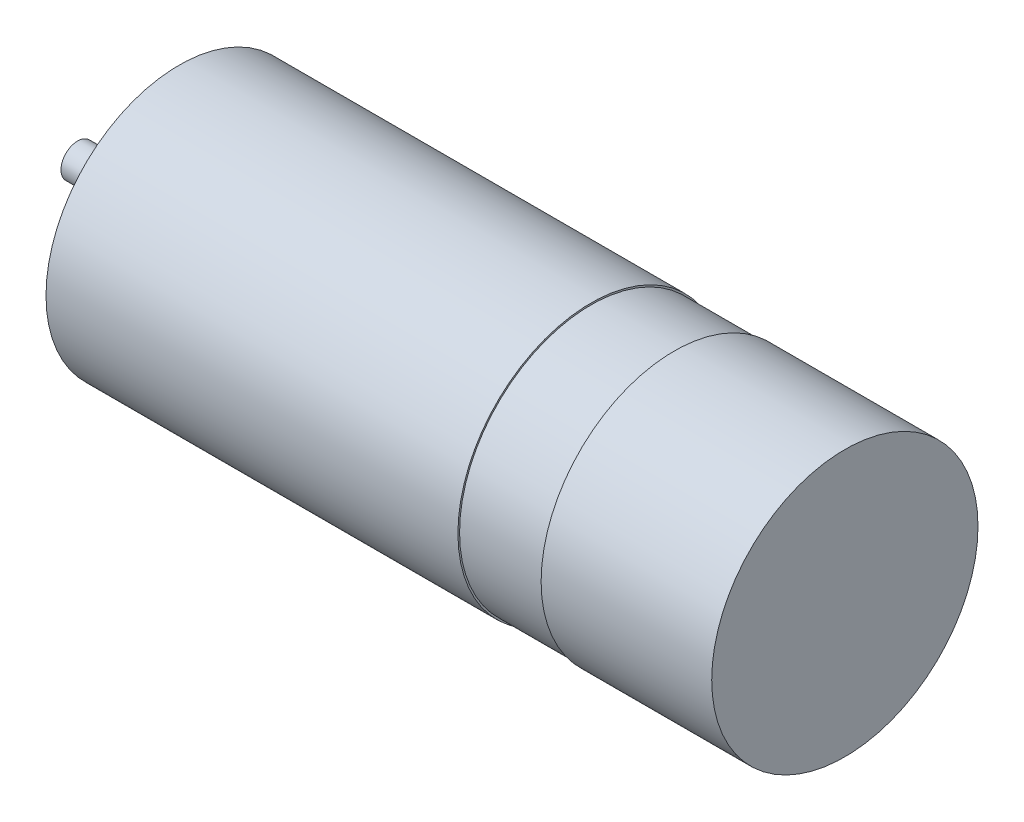
SolidWorks part; units mm, degrees
ref_plane "Front Plane" through (0, 0, 0) normal (0, 0, 1) x (1, 0, 0)
ref_plane "Top Plane" through (0, 0, 0) normal (0, 1, 0) x (1, 0, 0)
ref_plane "Right Plane" through (0, 0, 0) normal (1, 0, 0) x (0, 0, -1)
sketch "Sketch2" plane through (0, 0, 0) normal (0, 0, 1) x (1, 0, 0)
  line L0 (0, 0) -> (46.1, 0)
  line L2 (46.1, 0) -> (46.1, 8)
  line L3 (46.1, 8) -> (35.85, 8)
  line L4 (35.85, 8) -> (35.85, 7.9)
  line L7 (35.85, 7.9) -> (30.85, 7.9)
  line L9 (30.85, 7.9) -> (30.85, 8)
  line L10 (30.85, 8) -> (6.1, 8)
  line L12 (6.1, 8) -> (6.1, 4.5)
  line L13 (6.1, 4.5) -> (5.1, 4.5)
  line L14 (5.1, 4.5) -> (5.1, 1)
  line L15 (5.1, 1) -> (0, 1)
  line L16 (0, 1) -> (0, 0)
  dimension "D1" = 1
  dimension "D2" = 4.5
  dimension "D3" = 8
  dimension "D4" = 7.9
  dimension "D5" = 5.1
  dimension "D6" = 1
  dimension "D7" = 40
  dimension "D8" = 5
  dimension "D9" = 24.75
revolve "Revolve1" add sketch "Sketch2" angle 360 about L0
